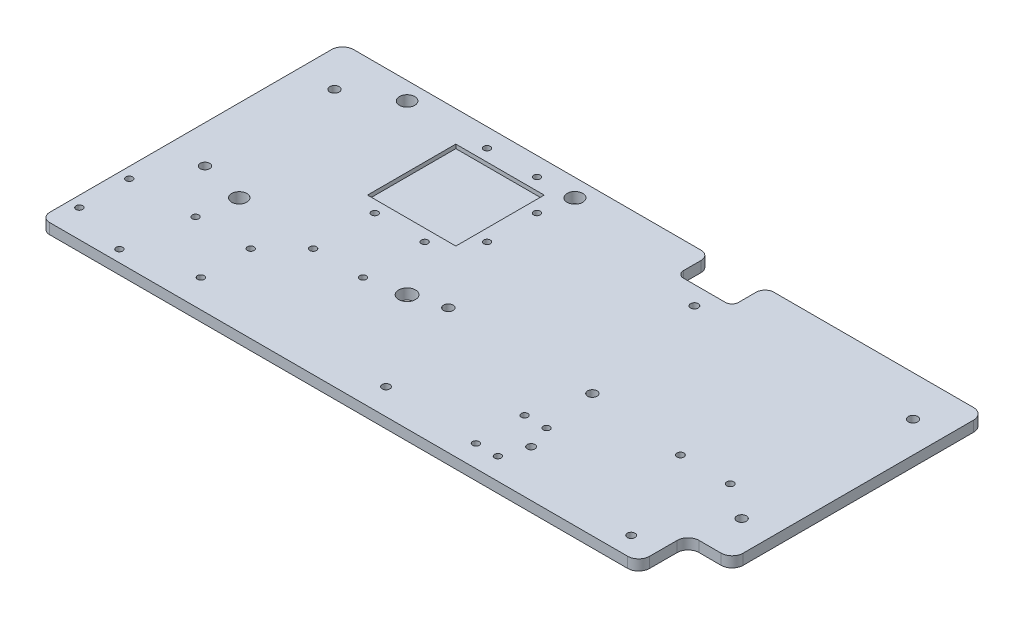
SolidWorks part; units mm, degrees
ref_plane "Front Plane" through (0, 0, 0) normal (0, 0, 1) x (1, 0, 0)
ref_plane "Top Plane" through (0, 0, 0) normal (0, 1, 0) x (1, 0, 0)
ref_plane "Right Plane" through (0, 0, 0) normal (1, 0, 0) x (0, 0, -1)
sketch "Sketch1" plane through (0, 0, 0) normal (0, 1, 0) x (1, 0, 0)
  line L0 (245, 5) -> (245, 17.4326)
  line L1 (0, 0) -> (240, 0)
  line L3 (-21.4195, 137) -> (136.363, 137)
  line L4 (265, 27.4326) -> (265, 132)
  line L5 (250, 22.4326) -> (260, 22.4326)
  line L10 (171.2, 32) -> (161.2, 32) construction
  line L11 (171.2, 32) -> (184.9823, 32) construction
  line L12 (184.9823, 9.902) -> (161.2, 9.902) construction
  line L13 (165.363, 125) -> (165.363, 133)
  line L14 (162.363, 122) -> (143.363, 122)
  line L15 (140.363, 125) -> (140.363, 133)
  line L16 (169.363, 137) -> (260, 137)
  line L17 (-46.41, 2.2674) -> (-46.41, 11.2476) construction
  line L18 (10.9233, 52.7456) -> (10.9233, 128.9456) construction
  line L19 (10.9233, 128.9456) -> (87.1233, 128.9456) construction
  line L20 (87.1233, 128.9456) -> (87.1233, 52.7456) construction
  line L21 (10.9233, 52.7456) -> (87.1233, 52.7456) construction
  line L22 (0, 0) -> (-22.4195, 0)
  line L23 (-46.41, 2.2674) -> (-46.41, 11.2476) construction
  line L25 (87.1233, 52.7456) -> (87.3201, 64.474) construction
  line L26 (-26.4195, 4) -> (-26.4195, 132)
  arc A0 (-21.4195, 137) -> (-26.4195, 132) centre (-21.4195, 132) ccw
  circle A1 centre (10.9233, 52.7456) radius 3.4419
  circle A2 centre (87.1233, 52.7456) radius 3.8197
  circle A3 centre (10.9233, 128.9456) radius 3.4785
  circle A4 centre (223.4922, 77.58) radius 13 construction
  circle A5 centre (87.1233, 128.9456) radius 3.546
  circle A6 centre (251.0553, 40.6931) radius 2.15
  circle A7 centre (250.9071, 118.6508) radius 2.15
  circle A8 centre (-9.3834, 57.4772) radius 2.15
  circle A9 centre (232.6, 9) radius 1.75
  circle A10 centre (-10.1099, 117.0187) radius 2.15
  circle A11 centre (175.0261, 21.1355) radius 1.75
  circle A12 centre (234.8207, 51.7688) radius 1.6
  circle A13 centre (212.1639, 51.7688) radius 1.6
  circle A16 centre (101.6128, 56.9929) radius 2.15
  circle A17 centre (168.0226, 55.9593) radius 2.15
  circle A18 centre (171.2, 32) radius 1.5
  circle A19 centre (171.2, 9.902) radius 1.5
  circle A20 centre (118.5, 11.8) radius 1.75
  circle A21 centre (161.2, 9.902) radius 1.5
  circle A22 centre (161.2, 32) radius 1.5
  circle A23 centre (156.7, 113.6) radius 1.75
  circle A27 centre (59, 103) radius 4.2574 construction
  circle A28 centre (84.495, 114.3284) radius 1.5
  circle A29 centre (84.495, 91.6716) radius 1.4224 construction
  circle A30 centre (84.495, 114.3284) radius 1.6764 construction
  circle A31 centre (84.495, 114.3284) radius 1.6764 construction
  circle A32 centre (84.495, 91.6716) radius 1.4224 construction
  circle A33 centre (84.495, 91.6716) radius 1.5
  circle A34 centre (70.3284, 77.505) radius 1.5
  circle A35 centre (47.6716, 77.505) radius 1.5
  arc A36 (140.363, 133) -> (136.363, 137) centre (136.363, 133) ccw
  arc A37 (165.363, 133) -> (169.363, 137) centre (169.363, 133) cw
  arc A38 (143.363, 122) -> (140.363, 125) centre (143.363, 125) cw
  arc A39 (165.363, 125) -> (162.363, 122) centre (162.363, 125) cw
  circle A40 centre (47.6716, 128.495) radius 1.5
  circle A41 centre (70.3284, 128.495) radius 1.5
  circle A42 centre (33.505, 12.7216) radius 1.5
  circle A43 centre (33.505, 35.3784) radius 1.5
  circle A44 centre (70.3284, 49.545) radius 1.5
  circle A45 centre (47.6716, 49.545) radius 1.5
  circle A46 centre (3.9, 5.3556) radius 1.5
  circle A47 centre (8.472, 35.353) radius 1.5
  arc A50 (-22.4195, 0) -> (-26.4195, 4) centre (-22.4195, 4) cw
  arc A51 (245, 5) -> (240, 0) centre (240, 5) cw
  arc A52 (245, 17.4326) -> (250, 22.4326) centre (250, 17.4326) cw
  arc A53 (260, 22.4326) -> (265, 27.4326) centre (260, 27.4326) ccw
  arc A54 (260, 137) -> (265, 132) centre (260, 132) cw
  circle A56 centre (-21.5412, 12.6186) radius 1.5
  circle A57 centre (-21.5412, 35.2754) radius 1.5
  spline S2 degree 3 poles (-20.5196, 35.3784) (-20.5196, 37.4612) (-22.6024, 37.4612) (-22.6024, 35.3784) (-22.6024, 33.2956) (-20.5196, 33.2956) (-20.5196, 35.3784) (-20.5196, 37.4612) (-22.6024, 37.4612) knots -0.5 0 0 0 0.5 0.5 0.5 1 1 1 1.5 1.5 1.5 weights 1 0.333333 0.333333 1 0.333333 0.333333 1 0.333333 0.333333 only from (-20.5196, 35.3784) to (-20.5196, 35.3784) construction
  spline S3 degree 3 poles (-20.5196, 35.3784) (-20.5196, 37.4612) (-22.6024, 37.4612) (-22.6024, 35.3784) (-22.6024, 33.2956) (-20.5196, 33.2956) (-20.5196, 35.3784) (-20.5196, 37.4612) (-22.6024, 37.4612) knots -0.5 0 0 0 0.5 0.5 0.5 1 1 1 1.5 1.5 1.5 weights 1 0.333333 0.333333 1 0.333333 0.333333 1 0.333333 0.333333 only from (-20.5196, 35.3784) to (-20.5196, 35.3784) construction
  point P101 (165.363, 137)
  point P104 (140.363, 122)
  point P107 (165.363, 122)
  point P149 (245, 22.4326)
  point P152 (265, 22.4326)
  point P155 (265, 137)
  point P158 (0, 137)
  dimension "D6" = 76.2
  dimension "D7" = 26
  dimension "D8" = 3.5
  dimension "D9" = 32.4
  dimension "D10" = 9
  dimension "D5" = 5
  dimension "D13" = 76.2
  dimension "D19" = 93.8
  dimension "D20" = 32
  dimension "D21" = 3
  dimension "D22" = 3
  dimension "D23" = 146.5
  dimension "D24" = 11.8
  dimension "D27" = 108.3
  dimension "D28" = 23.4
  dimension "D34" = 34
  dimension "D35" = 206
  dimension "D36" = 3
  dimension "D37" = 25
  dimension "D39" = 4
  dimension "D40" = 3
  dimension "D44" = 4
  dimension "D2" = 137
  dimension "D11" = 114.5674
  dimension "D12" = 20
  dimension "D25" = 10
  dimension "D26" = 10
  dimension "D38" = 15
extrude "Boss-Extrude1" add sketch "Sketch1" along normal blind 4.8
sketch "Sketch8" plane through (0, 4.8, 0) normal (0, 1, 0) x (1, 0, 0)
  line L8 (38.95, 82.95) -> (79.05, 82.95)
  line L9 (79.05, 82.95) -> (79.05, 123.05)
  line L10 (79.05, 123.05) -> (38.95, 123.05)
  line L11 (38.95, 123.05) -> (38.95, 82.95)
extrude "Cut-Extrude3" cut sketch "Sketch8" against normal blind 1.8
